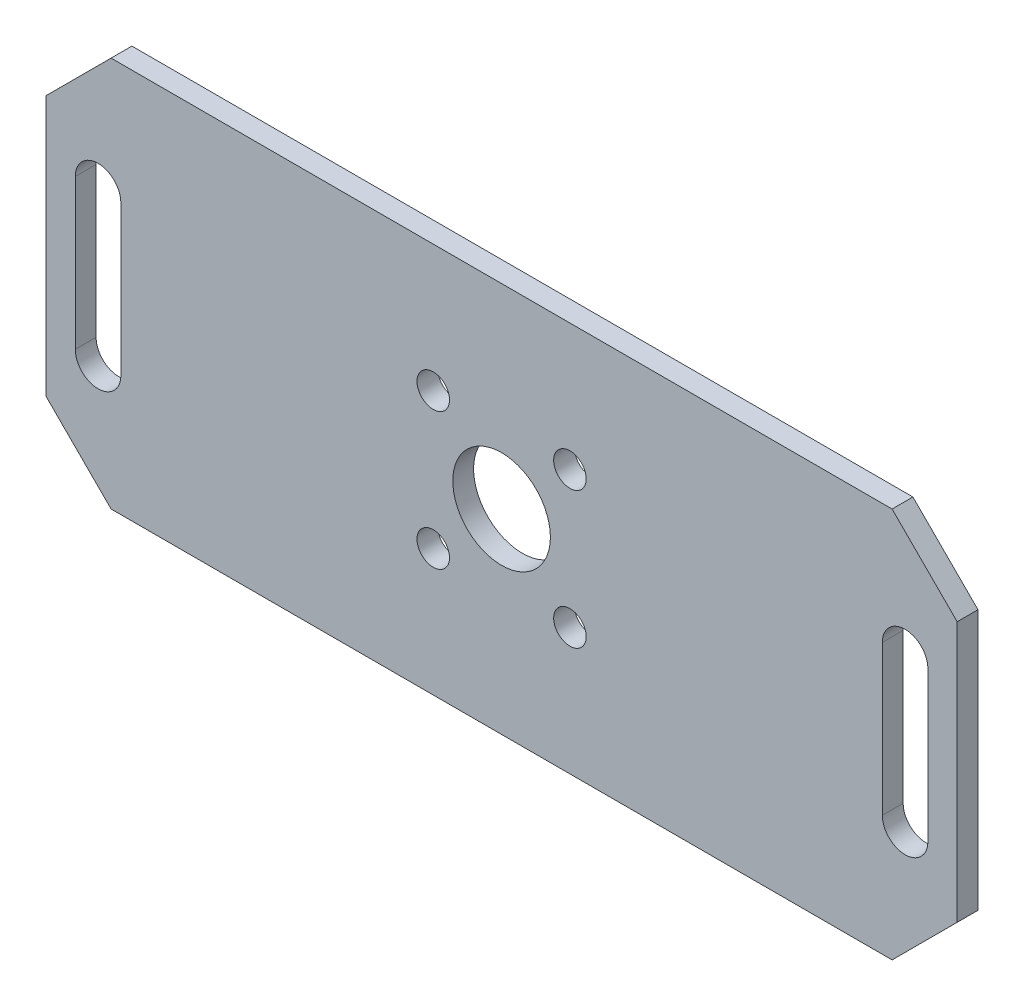
SolidWorks part; units mm, degrees
ref_plane "Front Plane" through (0, 0, 0) normal (0, 0, 1) x (1, 0, 0)
ref_plane "Top Plane" through (0, 0, 0) normal (0, 1, 0) x (1, 0, 0)
ref_plane "Right Plane" through (0, 0, 0) normal (1, 0, 0) x (0, 0, -1)
sketch "Sketch1" plane through (0, 0, 0) normal (0, 0, 1) x (1, 0, 0)
  line L0 (-1000, 0) -> (49000, 0) construction
  line L1 (-70, -30) -> (70, -30)
  line L2 (-70, -30) -> (-70, 30)
  line L3 (-70, 30) -> (70, 30)
  line L4 (70, -30) -> (70, 30)
  line L5 (-70, -30) -> (70, 30) construction
  line L6 (-70, 30) -> (70, -30) construction
  line L7 (-62, -11.5) -> (-62, 11.5) construction
  line L8 (-65.5, -11.5) -> (-65.5, 11.5)
  line L9 (-58.5, -11.5) -> (-58.5, 11.5)
  line L10 (62, -11.5) -> (62, 11.5) construction
  line L11 (58.5, -11.5) -> (58.5, 11.5)
  line L12 (65.5, -11.5) -> (65.5, 11.5)
  line L14 (-10.5, -10.5) -> (10.5, -10.5) construction
  line L15 (-10.5, -10.5) -> (-10.5, 10.5) construction
  line L16 (-10.5, 10.5) -> (10.5, 10.5) construction
  line L17 (10.5, -10.5) -> (10.5, 10.5) construction
  line L18 (-10.5, -10.5) -> (10.5, 10.5) construction
  line L19 (-10.5, 10.5) -> (10.5, -10.5) construction
  arc A0 (-65.5, -11.5) -> (-58.5, -11.5) centre (-62, -11.5) ccw
  arc A1 (-58.5, 11.5) -> (-65.5, 11.5) centre (-62, 11.5) ccw
  arc A2 (58.5, -11.5) -> (65.5, -11.5) centre (62, -11.5) ccw
  arc A3 (65.5, 11.5) -> (58.5, 11.5) centre (62, 11.5) ccw
  circle A4 centre (0, 0) radius 7.5
  circle A5 centre (-10.5, 10.5) radius 2.5
  circle A6 centre (10.5, 10.5) radius 2.5
  circle A7 centre (10.5, -10.5) radius 2.5
  circle A8 centre (-10.5, -10.5) radius 2.5
  point P0 (0, 0)
  point P10 (-62, 0)
  point P16 (62, 0)
  dimension "D9" = 15
  dimension "D12" = 5
  dimension "D5" = 7
  dimension "D1" = 140
  dimension "D2" = 60
  dimension "D3" = 62
  dimension "D4" = 62
  dimension "D6" = 7
  dimension "D7" = 23
  dimension "D8" = 23
  dimension "D10" = 21
  dimension "D11" = 21
extrude "Boss-Extrude1" add sketch "Sketch1" along normal blind 3.2
chamfer "Chamfer1" distance 10 angle 45 4 edges at (-70, -30, 1.6) (70, -30, 1.6) (70, 30, 1.6) (-70, 30, 1.6)
